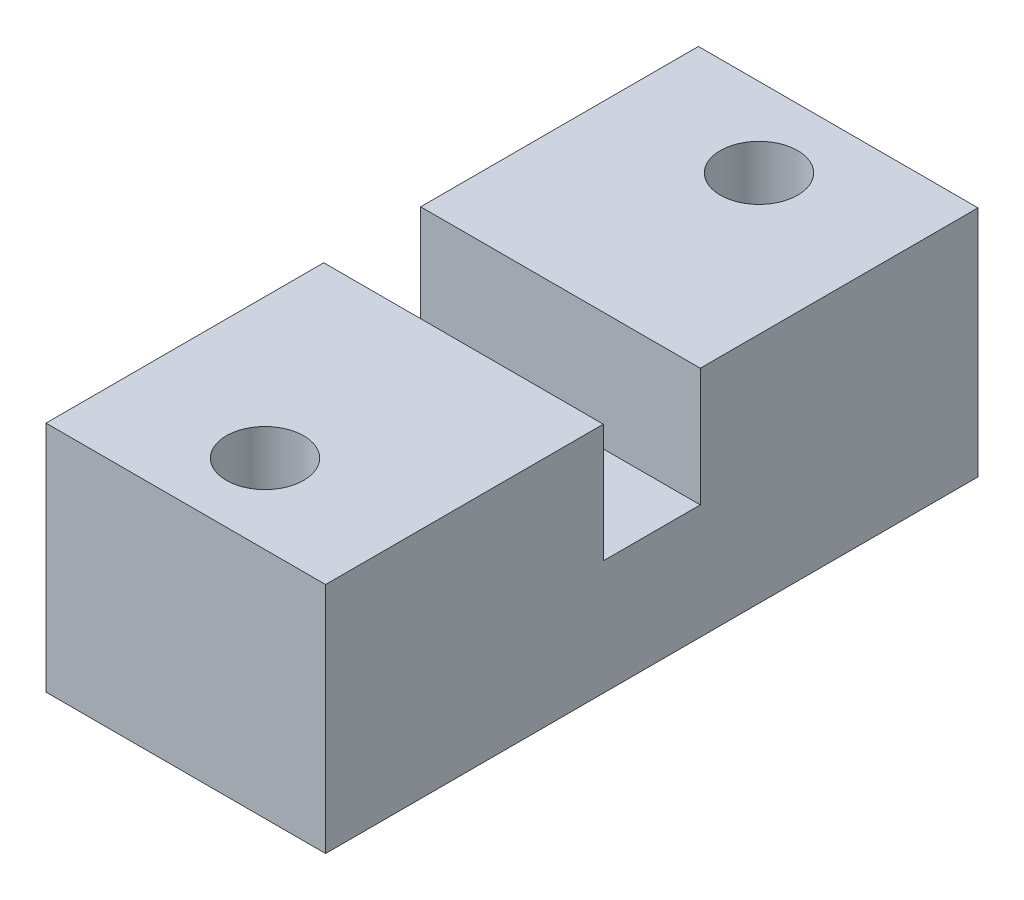
SolidWorks part; units mm, degrees
ref_plane "Спереди" through (0, 0, 0) normal (0, 0, 1) x (1, 0, 0)
ref_plane "Сверху" through (0, 0, 0) normal (0, 1, 0) x (1, 0, 0)
ref_plane "Справа" through (0, 0, 0) normal (1, 0, 0) x (0, 0, -1)
sketch "Sketch1" plane through (0, 0, 0) normal (0, 1, 0) x (1, 0, 0)
  line L1 (15, -35) -> (-15, -35)
  line L2 (15, -35) -> (15, 35)
  line L3 (15, 35) -> (-15, 35)
  line L4 (-15, -35) -> (-15, 35)
  line L5 (15, -35) -> (-15, 35) construction
  line L6 (15, 35) -> (-15, -35) construction
  point P0 (0, 0)
  dimension "D1" = 30
  dimension "D2" = 70
extrude "Boss-Extrude1" add sketch "Sketch1" along normal blind 25
sketch "Sketch2" plane through (0, 25, 0) normal (0, 1, 0) x (1, 0, 0)
  line L0 (-15, 35) -> (-15, -35) construction
  line L1 (15, -5.2) -> (-15, -5.2)
  line L2 (15, -5.2) -> (15, 5.2)
  line L3 (15, 5.2) -> (-15, 5.2)
  line L4 (-15, -5.2) -> (-15, 5.2)
  line L5 (15, -5.2) -> (-15, 5.2) construction
  line L6 (15, 5.2) -> (-15, -5.2) construction
  point P0 (0, 0)
  dimension "D1" = 10.4
extrude "Cut-Extrude1" cut sketch "Sketch2" against normal blind 12.7
sketch "Sketch3" plane through (0, 25, 0) normal (0, 1, 0) x (1, 0, 0)
  line L0 (0, 35) -> (0, -35) construction
  line L1 (15, 35) -> (-15, 35) construction
  line L2 (-15, -35) -> (15, -35) construction
  circle A0 centre (0, 26.5) radius 4.15
  circle A1 centre (0, -26.5) radius 4.15
  point P10 (0, 0)
  dimension "D1" = 8.3
  dimension "D2" = 53
  dimension "D3" = 26.5
extrude "Cut-Extrude2" cut sketch "Sketch3" against normal through all
chamfer "Chamfer1" distance 1 angle 50 2 edges at (0, 0, 30.65) (0, 0, -22.35)
